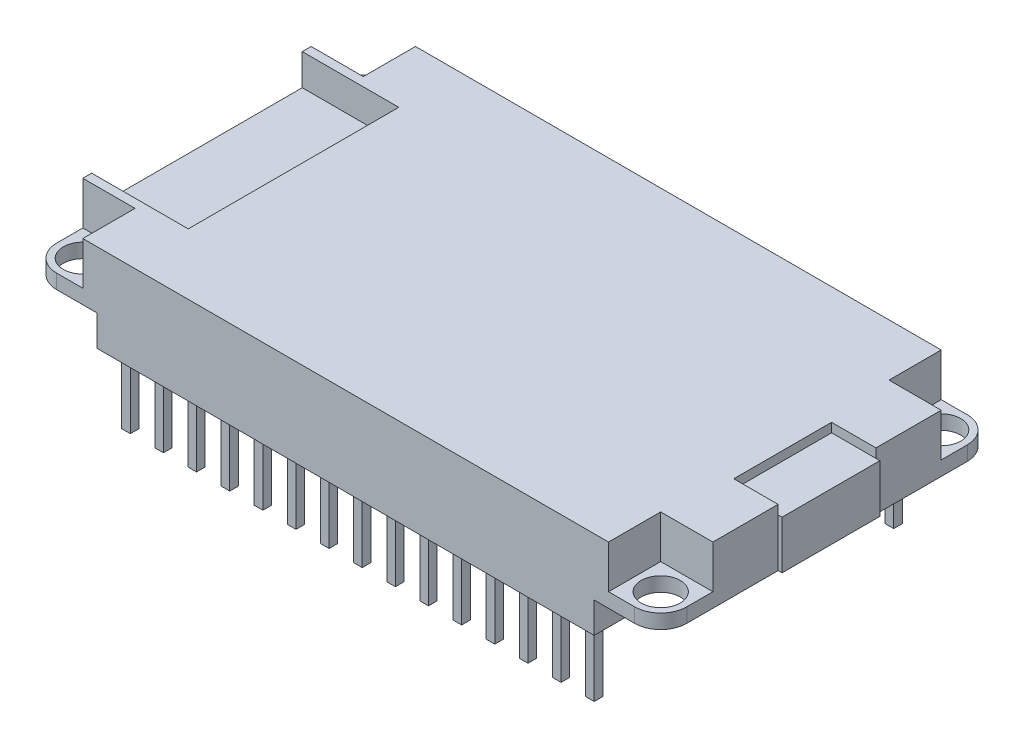
SolidWorks part; units mm, degrees
ref_plane "Front Plane" through (0, 0, 0) normal (0, 0, 1) x (1, 0, 0)
ref_plane "Top Plane" through (0, 0, 0) normal (0, 1, 0) x (1, 0, 0)
ref_plane "Right Plane" through (0, 0, 0) normal (1, 0, 0) x (0, 0, -1)
sketch "Sketch1" plane through (0, 0, 0) normal (0, 1, 0) x (1, 0, 0)
  line L0 (24.15, 0) -> (24.15, -25.5) construction
  line L1 (0, 0) -> (48.3, 0)
  line L2 (0, 0) -> (0, -25.5)
  line L3 (0, -25.5) -> (48.3, -25.5)
  line L4 (48.3, 0) -> (48.3, -25.5)
  line L5 (0, -12.75) -> (48.3, -12.75) construction
  line L6 (0, -25.5) -> (48.3, -25.5)
  circle A0 centre (2, -2) radius 1.5
  circle A1 centre (46.3, -2) radius 1.5
  circle A2 centre (46.3, -23.5) radius 1.5
  circle A3 centre (2, -23.5) radius 1.5
  dimension "D3" = 3
  dimension "D4" = 2
  dimension "D5" = 2
  dimension "D1" = 48.3
  dimension "D2" = 25.5
extrude "Boss-Extrude1" add sketch "Sketch1" along normal blind 4.4 contours L4 L1 L2 L3 A1 A0 A2 A3
fillet "Fillet1" radius 2 4 edges at (0, 2.2, 0) (48.3, 2.2, 0) (48.3, 2.2, 25.5) (0, 2.2, 25.5)
sketch "Sketch2" plane through (0, 0, 0) normal (0, -1, 0) x (1, 0, 0)
  line L0 (2, 25.5) -> (46.3, 25.5) construction
  line L1 (5.1, 25.5) -> (7.64, 25.5)
  line L2 (5.1, 25.5) -> (5.1, 22.96)
  line L3 (5.1, 22.96) -> (7.64, 22.96)
  line L4 (7.64, 25.5) -> (7.64, 22.96)
  line L5 (0, 2) -> (0, 23.5) construction
  line L6 (7.64, 25.5) -> (7.64, 22.96)
  line L7 (7.64, 25.5) -> (10.18, 25.5)
  line L8 (10.18, 25.5) -> (10.18, 22.96)
  line L9 (7.64, 22.96) -> (10.18, 22.96)
  line L10 (10.18, 25.5) -> (10.18, 22.96)
  line L11 (10.18, 25.5) -> (12.72, 25.5)
  line L12 (12.72, 25.5) -> (12.72, 22.96)
  line L13 (10.18, 22.96) -> (12.72, 22.96)
  line L14 (12.72, 25.5) -> (12.72, 22.96)
  line L15 (12.72, 25.5) -> (15.26, 25.5)
  line L16 (15.26, 25.5) -> (15.26, 22.96)
  line L17 (12.72, 22.96) -> (15.26, 22.96)
  line L18 (15.26, 25.5) -> (15.26, 22.96)
  line L19 (15.26, 25.5) -> (17.8, 25.5)
  line L20 (17.8, 25.5) -> (17.8, 22.96)
  line L21 (15.26, 22.96) -> (17.8, 22.96)
  line L22 (17.8, 25.5) -> (17.8, 22.96)
  line L23 (17.8, 25.5) -> (20.34, 25.5)
  line L24 (20.34, 25.5) -> (20.34, 22.96)
  line L25 (17.8, 22.96) -> (20.34, 22.96)
  line L26 (20.34, 25.5) -> (20.34, 22.96)
  line L27 (20.34, 25.5) -> (22.88, 25.5)
  line L28 (22.88, 25.5) -> (22.88, 22.96)
  line L29 (20.34, 22.96) -> (22.88, 22.96)
  line L30 (22.88, 25.5) -> (22.88, 22.96)
  line L31 (22.88, 25.5) -> (25.42, 25.5)
  line L32 (25.42, 25.5) -> (25.42, 22.96)
  line L33 (22.88, 22.96) -> (25.42, 22.96)
  line L34 (25.42, 25.5) -> (25.42, 22.96)
  line L35 (25.42, 25.5) -> (27.96, 25.5)
  line L36 (27.96, 25.5) -> (27.96, 22.96)
  line L37 (25.42, 22.96) -> (27.96, 22.96)
  line L38 (27.96, 25.5) -> (27.96, 22.96)
  line L39 (27.96, 25.5) -> (30.5, 25.5)
  line L40 (30.5, 25.5) -> (30.5, 22.96)
  line L41 (27.96, 22.96) -> (30.5, 22.96)
  line L42 (30.5, 25.5) -> (30.5, 22.96)
  line L43 (30.5, 25.5) -> (33.04, 25.5)
  line L44 (33.04, 25.5) -> (33.04, 22.96)
  line L45 (30.5, 22.96) -> (33.04, 22.96)
  line L46 (33.04, 25.5) -> (33.04, 22.96)
  line L47 (33.04, 25.5) -> (35.58, 25.5)
  line L48 (35.58, 25.5) -> (35.58, 22.96)
  line L49 (33.04, 22.96) -> (35.58, 22.96)
  line L50 (35.58, 25.5) -> (35.58, 22.96)
  line L51 (35.58, 25.5) -> (38.12, 25.5)
  line L52 (38.12, 25.5) -> (38.12, 22.96)
  line L53 (35.58, 22.96) -> (38.12, 22.96)
  line L54 (38.12, 25.5) -> (38.12, 22.96)
  line L55 (38.12, 25.5) -> (40.66, 25.5)
  line L56 (40.66, 25.5) -> (40.66, 22.96)
  line L57 (38.12, 22.96) -> (40.66, 22.96)
  line L58 (40.66, 25.5) -> (40.66, 22.96)
  line L59 (40.66, 25.5) -> (43.2, 25.5)
  line L60 (43.2, 25.5) -> (43.2, 22.96)
  line L61 (40.66, 22.96) -> (43.2, 22.96)
  line L62 (48.3, 2) -> (48.3, 23.5) construction
  line L63 (0, 12.75) -> (48.3, 12.75) construction
  line L64 (40.66, 2.54) -> (43.2, 2.54)
  line L65 (43.2, 0) -> (43.2, 2.54)
  line L66 (40.66, 0) -> (43.2, 0)
  line L67 (40.66, 0) -> (40.66, 2.54)
  line L68 (38.12, 2.54) -> (40.66, 2.54)
  line L69 (40.66, 0) -> (40.66, 2.54)
  line L70 (38.12, 0) -> (40.66, 0)
  line L71 (38.12, 0) -> (38.12, 2.54)
  line L72 (35.58, 2.54) -> (38.12, 2.54)
  line L73 (38.12, 0) -> (38.12, 2.54)
  line L74 (35.58, 0) -> (38.12, 0)
  line L75 (35.58, 0) -> (35.58, 2.54)
  line L76 (33.04, 2.54) -> (35.58, 2.54)
  line L77 (35.58, 0) -> (35.58, 2.54)
  line L78 (33.04, 0) -> (35.58, 0)
  line L79 (33.04, 0) -> (33.04, 2.54)
  line L80 (30.5, 2.54) -> (33.04, 2.54)
  line L81 (33.04, 0) -> (33.04, 2.54)
  line L82 (30.5, 0) -> (33.04, 0)
  line L83 (30.5, 0) -> (30.5, 2.54)
  line L84 (27.96, 2.54) -> (30.5, 2.54)
  line L85 (30.5, 0) -> (30.5, 2.54)
  line L86 (27.96, 0) -> (30.5, 0)
  line L87 (27.96, 0) -> (27.96, 2.54)
  line L88 (25.42, 2.54) -> (27.96, 2.54)
  line L89 (27.96, 0) -> (27.96, 2.54)
  line L90 (25.42, 0) -> (27.96, 0)
  line L91 (25.42, 0) -> (25.42, 2.54)
  line L92 (22.88, 2.54) -> (25.42, 2.54)
  line L93 (25.42, 0) -> (25.42, 2.54)
  line L94 (22.88, 0) -> (25.42, 0)
  line L95 (22.88, 0) -> (22.88, 2.54)
  line L96 (20.34, 2.54) -> (22.88, 2.54)
  line L97 (22.88, 0) -> (22.88, 2.54)
  line L98 (20.34, 0) -> (22.88, 0)
  line L99 (20.34, 0) -> (20.34, 2.54)
  line L100 (17.8, 2.54) -> (20.34, 2.54)
  line L101 (20.34, 0) -> (20.34, 2.54)
  line L102 (17.8, 0) -> (20.34, 0)
  line L103 (17.8, 0) -> (17.8, 2.54)
  line L104 (15.26, 2.54) -> (17.8, 2.54)
  line L105 (17.8, 0) -> (17.8, 2.54)
  line L106 (15.26, 0) -> (17.8, 0)
  line L107 (15.26, 0) -> (15.26, 2.54)
  line L108 (12.72, 2.54) -> (15.26, 2.54)
  line L109 (15.26, 0) -> (15.26, 2.54)
  line L110 (12.72, 0) -> (15.26, 0)
  line L111 (12.72, 0) -> (12.72, 2.54)
  line L112 (10.18, 2.54) -> (12.72, 2.54)
  line L113 (12.72, 0) -> (12.72, 2.54)
  line L114 (10.18, 0) -> (12.72, 0)
  line L115 (10.18, 0) -> (10.18, 2.54)
  line L116 (7.64, 2.54) -> (10.18, 2.54)
  line L117 (10.18, 0) -> (10.18, 2.54)
  line L118 (7.64, 0) -> (10.18, 0)
  line L119 (7.64, 0) -> (7.64, 2.54)
  line L120 (7.64, 0) -> (7.64, 2.54)
  line L121 (5.1, 2.54) -> (7.64, 2.54)
  line L122 (5.1, 0) -> (5.1, 2.54)
  line L123 (5.1, 0) -> (7.64, 0)
  line M66 (2, 0) -> (46.3, 0)
  line M70 (46.3, 25.5) -> (2, 25.5)
  dimension "D1" = 2.54
  dimension "D2" = 2.54
  dimension "D3" = 5.1
  dimension "D6" = 5.1
  dimension "D4" = 15
extrude "Boss-Extrude2" add sketch "Sketch2" along normal blind 2.35 contours L4 L2 L3 M70 | L4 L9 L8 M70 | L8 L13 L12 M70 | L12 L17 L16 M70 | L16 L21 L20 M70 | L20 L25 L24 M70 | L24 L29 L28 M70 | L28 L33 L32 M70 | L32 L37 L36 M70 | L36 L41 L40 M70 | L40 L45 L44 M70 | L44 L49 L48 M70 | L48 L53 L52 M70 | L52 L57 L56 M70 | L56 L61 L60 M70 | L67 L65 L64 M66 | L71 L67 L68 M66 | L75 L71 L72 M66 | L79 L75 L76 M66 | L83 L79 L80 M66 | L87 L83 L84 M66 | L91 L87 L88 M66 | L95 L91 L92 M66 | L99 L95 L96 M66 | L103 L99 L100 M66 | L107 L103 L104 M66 | L111 L107 L108 M66 | L115 L111 L112 M66 | L119 L115 L116 M66 | L122 L119 L121 M66
sketch "Sketch3" plane through (0, -2.35, 0) normal (0, -1, 0) x (1, 0, 0)
  line L0 (7.64, 25.5) -> (7.64, 22.96) construction
  line L1 (6.04, 24.56) -> (6.7, 24.56)
  line L2 (6.04, 24.56) -> (6.04, 23.9)
  line L3 (6.04, 23.9) -> (6.7, 23.9)
  line L4 (6.7, 24.56) -> (6.7, 23.9)
  line L5 (43.2, 25.5) -> (5.1, 25.5) construction
  line L6 (5.1, 22.96) -> (43.2, 22.96) construction
  line L7 (5.1, 25.5) -> (5.1, 22.96) construction
  line L8 (6.04, 24.56) -> (5.1, 24.56) construction
  line L9 (6.7, 24.56) -> (7.64, 24.56) construction
  line L10 (6.04, 24.56) -> (6.04, 25.5) construction
  line L11 (6.04, 23.9) -> (6.04, 22.96) construction
  line L12 (5.1, 22.96) -> (43.2, 22.96) construction
  line L13 (8.58, 24.56) -> (8.58, 23.9)
  line L14 (8.58, 24.56) -> (9.24, 24.56)
  line L15 (9.24, 24.56) -> (9.24, 23.9)
  line L16 (8.58, 23.9) -> (9.24, 23.9)
  line L17 (11.12, 24.56) -> (11.12, 23.9)
  line L18 (11.12, 24.56) -> (11.78, 24.56)
  line L19 (11.78, 24.56) -> (11.78, 23.9)
  line L20 (11.12, 23.9) -> (11.78, 23.9)
  line L21 (13.66, 24.56) -> (13.66, 23.9)
  line L22 (13.66, 24.56) -> (14.32, 24.56)
  line L23 (14.32, 24.56) -> (14.32, 23.9)
  line L24 (13.66, 23.9) -> (14.32, 23.9)
  line L25 (16.2, 24.56) -> (16.2, 23.9)
  line L26 (16.2, 24.56) -> (16.86, 24.56)
  line L27 (16.86, 24.56) -> (16.86, 23.9)
  line L28 (16.2, 23.9) -> (16.86, 23.9)
  line L29 (18.74, 24.56) -> (18.74, 23.9)
  line L30 (18.74, 24.56) -> (19.4, 24.56)
  line L31 (19.4, 24.56) -> (19.4, 23.9)
  line L32 (18.74, 23.9) -> (19.4, 23.9)
  line L33 (21.28, 24.56) -> (21.28, 23.9)
  line L34 (21.28, 24.56) -> (21.94, 24.56)
  line L35 (21.94, 24.56) -> (21.94, 23.9)
  line L36 (21.28, 23.9) -> (21.94, 23.9)
  line L37 (23.82, 24.56) -> (23.82, 23.9)
  line L38 (23.82, 24.56) -> (24.48, 24.56)
  line L39 (24.48, 24.56) -> (24.48, 23.9)
  line L40 (23.82, 23.9) -> (24.48, 23.9)
  line L41 (26.36, 24.56) -> (26.36, 23.9)
  line L42 (26.36, 24.56) -> (27.02, 24.56)
  line L43 (27.02, 24.56) -> (27.02, 23.9)
  line L44 (26.36, 23.9) -> (27.02, 23.9)
  line L45 (28.9, 24.56) -> (28.9, 23.9)
  line L46 (28.9, 24.56) -> (29.56, 24.56)
  line L47 (29.56, 24.56) -> (29.56, 23.9)
  line L48 (28.9, 23.9) -> (29.56, 23.9)
  line L49 (31.44, 24.56) -> (31.44, 23.9)
  line L50 (31.44, 24.56) -> (32.1, 24.56)
  line L51 (32.1, 24.56) -> (32.1, 23.9)
  line L52 (31.44, 23.9) -> (32.1, 23.9)
  line L53 (33.98, 24.56) -> (33.98, 23.9)
  line L54 (33.98, 24.56) -> (34.64, 24.56)
  line L55 (34.64, 24.56) -> (34.64, 23.9)
  line L56 (33.98, 23.9) -> (34.64, 23.9)
  line L57 (36.52, 24.56) -> (36.52, 23.9)
  line L58 (36.52, 24.56) -> (37.18, 24.56)
  line L59 (37.18, 24.56) -> (37.18, 23.9)
  line L60 (36.52, 23.9) -> (37.18, 23.9)
  line L61 (39.06, 24.56) -> (39.06, 23.9)
  line L62 (39.06, 24.56) -> (39.72, 24.56)
  line L63 (39.72, 24.56) -> (39.72, 23.9)
  line L64 (39.06, 23.9) -> (39.72, 23.9)
  line L65 (41.6, 24.56) -> (41.6, 23.9)
  line L66 (41.6, 24.56) -> (42.26, 24.56)
  line L67 (42.26, 24.56) -> (42.26, 23.9)
  line L68 (41.6, 23.9) -> (42.26, 23.9)
  line L69 (0, 12.75) -> (48.3, 12.75) construction
  line L70 (0, 2) -> (0, 23.5) construction
  line L71 (48.3, 2) -> (48.3, 23.5) construction
  line L72 (6.04, 1.6) -> (6.04, 2.54) construction
  line L73 (6.04, 0.94) -> (6.04, 0) construction
  line L74 (6.7, 0.94) -> (7.64, 0.94) construction
  line L75 (6.04, 0.94) -> (5.1, 0.94) construction
  line L76 (7.64, 0) -> (7.64, 2.54) construction
  line L77 (41.6, 1.6) -> (42.26, 1.6)
  line L78 (42.26, 0.94) -> (42.26, 1.6)
  line L79 (41.6, 0.94) -> (42.26, 0.94)
  line L80 (41.6, 0.94) -> (41.6, 1.6)
  line L81 (39.06, 1.6) -> (39.72, 1.6)
  line L82 (39.72, 0.94) -> (39.72, 1.6)
  line L83 (39.06, 0.94) -> (39.72, 0.94)
  line L84 (39.06, 0.94) -> (39.06, 1.6)
  line L85 (36.52, 1.6) -> (37.18, 1.6)
  line L86 (37.18, 0.94) -> (37.18, 1.6)
  line L87 (36.52, 0.94) -> (37.18, 0.94)
  line L88 (36.52, 0.94) -> (36.52, 1.6)
  line L89 (33.98, 1.6) -> (34.64, 1.6)
  line L90 (34.64, 0.94) -> (34.64, 1.6)
  line L91 (33.98, 0.94) -> (34.64, 0.94)
  line L92 (33.98, 0.94) -> (33.98, 1.6)
  line L93 (31.44, 1.6) -> (32.1, 1.6)
  line L94 (32.1, 0.94) -> (32.1, 1.6)
  line L95 (31.44, 0.94) -> (32.1, 0.94)
  line L96 (31.44, 0.94) -> (31.44, 1.6)
  line L97 (28.9, 1.6) -> (29.56, 1.6)
  line L98 (29.56, 0.94) -> (29.56, 1.6)
  line L99 (28.9, 0.94) -> (29.56, 0.94)
  line L100 (28.9, 0.94) -> (28.9, 1.6)
  line L101 (26.36, 1.6) -> (27.02, 1.6)
  line L102 (27.02, 0.94) -> (27.02, 1.6)
  line L103 (26.36, 0.94) -> (27.02, 0.94)
  line L104 (26.36, 0.94) -> (26.36, 1.6)
  line L105 (23.82, 1.6) -> (24.48, 1.6)
  line L106 (24.48, 0.94) -> (24.48, 1.6)
  line L107 (23.82, 0.94) -> (24.48, 0.94)
  line L108 (23.82, 0.94) -> (23.82, 1.6)
  line L109 (21.28, 1.6) -> (21.94, 1.6)
  line L110 (21.94, 0.94) -> (21.94, 1.6)
  line L111 (21.28, 0.94) -> (21.94, 0.94)
  line L112 (21.28, 0.94) -> (21.28, 1.6)
  line L113 (18.74, 1.6) -> (19.4, 1.6)
  line L114 (19.4, 0.94) -> (19.4, 1.6)
  line L115 (18.74, 0.94) -> (19.4, 0.94)
  line L116 (18.74, 0.94) -> (18.74, 1.6)
  line L117 (16.2, 1.6) -> (16.86, 1.6)
  line L118 (16.86, 0.94) -> (16.86, 1.6)
  line L119 (16.2, 0.94) -> (16.86, 0.94)
  line L120 (16.2, 0.94) -> (16.2, 1.6)
  line L121 (13.66, 1.6) -> (14.32, 1.6)
  line L122 (14.32, 0.94) -> (14.32, 1.6)
  line L123 (13.66, 0.94) -> (14.32, 0.94)
  line L124 (13.66, 0.94) -> (13.66, 1.6)
  line L125 (11.12, 1.6) -> (11.78, 1.6)
  line L126 (11.78, 0.94) -> (11.78, 1.6)
  line L127 (11.12, 0.94) -> (11.78, 0.94)
  line L128 (11.12, 0.94) -> (11.12, 1.6)
  line L129 (8.58, 1.6) -> (9.24, 1.6)
  line L130 (9.24, 0.94) -> (9.24, 1.6)
  line L131 (8.58, 0.94) -> (9.24, 0.94)
  line L132 (8.58, 0.94) -> (8.58, 1.6)
  line L133 (6.7, 0.94) -> (6.7, 1.6)
  line L134 (6.04, 1.6) -> (6.7, 1.6)
  line L135 (6.04, 0.94) -> (6.04, 1.6)
  line L136 (6.04, 0.94) -> (6.7, 0.94)
  dimension "D1" = 0.66
  dimension "D2" = 0.66
  dimension "D3" = 2.54
  dimension "D5" = 2.54
  dimension "D4" = 15
extrude "Boss-Extrude3" add sketch "Sketch3" along normal blind 5.33
sketch "Sketch4" plane through (0, 4.4, 0) normal (0, 1, 0) x (1, 0, 0)
  line L0 (48.3, -2) -> (48.3, -23.5) construction
  line L1 (48.3, -9) -> (44.9, -9)
  line L2 (48.3, -9) -> (48.3, -16.5)
  line L3 (48.3, -16.5) -> (44.9, -16.5)
  line L4 (44.9, -9) -> (44.9, -16.5)
  line L5 (48.3, -12.75) -> (44.9, -12.75) construction
  dimension "D1" = 3.4
  dimension "D2" = 7.5
extrude "Cut-Extrude1" cut sketch "Sketch4" against normal offset from surface (0.7 mm away) 3.7 up to face at (2, 0, 25)
sketch "Sketch5" plane through (48.3, 0, 0) normal (1, 0, 0) x (0, 0, -1)
  line L0 (-2, 0) -> (-23.5, 0) construction
  line L1 (-16.5, 3.7) -> (-9, 3.7)
  line L2 (-16.5, 3.7) -> (-16.5, 0)
  line L3 (-16.5, 0) -> (-9, 0)
  line L4 (-9, 3.7) -> (-9, 0)
extrude "Boss-Extrude4" add sketch "Sketch5" along normal blind 0.3
sketch "Sketch6" plane through (0, 4.4, 0) normal (0, 1, 0) x (1, 0, 0)
  line L0 (0, -2) -> (0, -23.5) construction
  line L1 (0, -4.68) -> (7.4, -4.68)
  line L2 (0, -4.68) -> (0, -20.82)
  line L3 (0, -20.82) -> (7.4, -20.82)
  line L4 (7.4, -4.68) -> (7.4, -20.82)
  line L5 (0, -12.75) -> (7.4, -12.75) construction
  dimension "D1" = 16.14
  dimension "D2" = 7.4
extrude "Cut-Extrude2" cut sketch "Sketch6" against normal offset from surface (2.4 mm away) 2 up to face at (2, 0, 25)
sketch "Sketch7" plane through (0, 4.4, 0) normal (0, 1, 0) x (1, 0, 0)
  line L0 (0, -12.75) -> (48.6, -12.75) construction
  line L1 (4, -4) -> (0, -4)
  line L2 (4, -4) -> (4, 0)
  line L3 (4, 0) -> (0, 0)
  line L4 (0, -4) -> (0, 0)
  line L5 (0, -20.82) -> (0, -4.68) construction
  line L6 (48.6, -9) -> (48.6, -16.5) construction
  line L7 (24.15, 0) -> (24.15, -25.5) construction
  line L8 (2, 0) -> (46.3, 0) construction
  line L9 (2, -25.5) -> (46.3, -25.5) construction
  line L10 (44.3, 0) -> (48.3, 0)
  line L11 (48.3, -4) -> (48.3, 0)
  line L12 (44.3, -4) -> (48.3, -4)
  line L13 (44.3, -4) -> (44.3, 0)
  line L14 (44.3, -21.5) -> (44.3, -25.5)
  line L15 (44.3, -21.5) -> (48.3, -21.5)
  line L16 (48.3, -21.5) -> (48.3, -25.5)
  line L17 (44.3, -25.5) -> (48.3, -25.5)
  line L18 (4, -25.5) -> (0, -25.5)
  line L19 (0, -21.5) -> (0, -25.5)
  line L20 (4, -21.5) -> (0, -21.5)
  line L21 (4, -21.5) -> (4, -25.5)
  dimension "D1" = 4
  dimension "D2" = 4
extrude "Cut-Extrude3" cut sketch "Sketch7" against normal offset from surface (3.3 mm away) 1.1 up to face at (2, 0, 25)
